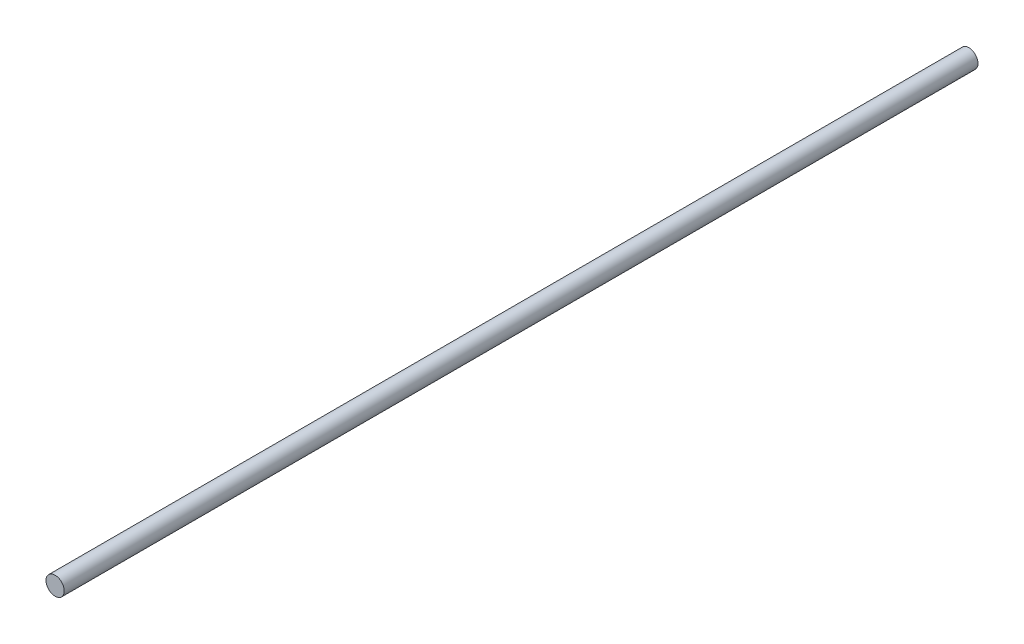
SolidWorks part; units mm, degrees
ref_plane "Front Plane" through (0, 0, 0) normal (0, 0, 1) x (1, 0, 0)
ref_plane "Top Plane" through (0, 0, 0) normal (0, 1, 0) x (1, 0, 0)
ref_plane "Right Plane" through (0, 0, 0) normal (1, 0, 0) x (0, 0, -1)
sketch "Sketch1" plane through (0, 0, 0) normal (0, 0, 1) x (1, 0, 0)
  circle A0 centre (0, 0) radius 4
  dimension "D1" = 8
extrude "Boss-Extrude1" add sketch "Sketch1" against normal blind 400
sketch "Sketch2" plane through (0, 0, 0) normal (0, 0, 1) x (1, 0, 0)
  circle A0 centre (0, 0) radius 4
  dimension "D1" = 8
curve "Helix/Spiral1" pitch 2 height 400 turns 200
